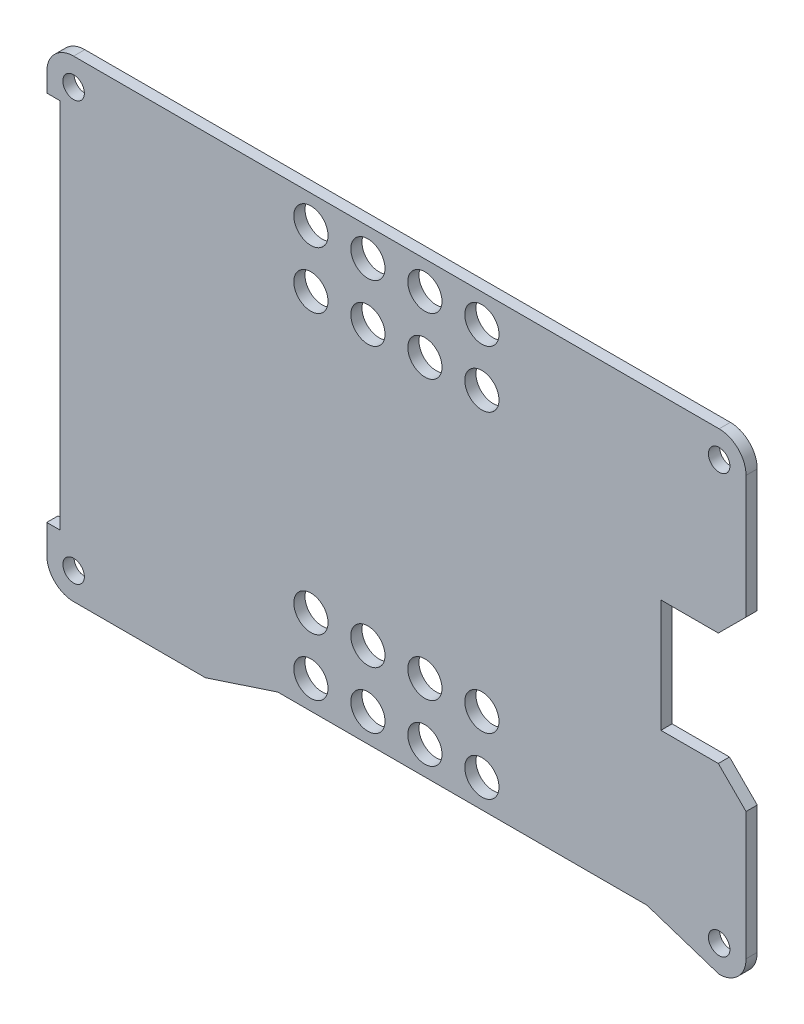
SolidWorks part; units mm, degrees
ref_plane "Front Plane" through (0, 0, 0) normal (0, 0, 1) x (1, 0, 0)
ref_plane "Top Plane" through (0, 0, 0) normal (0, 1, 0) x (1, 0, 0)
ref_plane "Right Plane" through (0, 0, 0) normal (1, 0, 0) x (0, 0, -1)
sketch "Sketch1" plane through (0, 0, 0) normal (0, 0, 1) x (1, 0, 0)
  line L0 (-301.9473, 111.7465) -> (-305.8779, 115.6771) construction
  line L1 (-305.8779, 115.6771) -> (-316.1078, 115.6771) construction
  line L2 (-316.1078, 115.6771) -> (-316.1078, 128.8851) construction
  line L3 (-316.1078, 128.8851) -> (-305.8779, 128.8851) construction
  line L4 (-305.8779, 128.8851) -> (-301.9473, 132.8157) construction
  line L5 (-301.9473, 132.8157) -> (-301.9473, 150.9704) construction
  line L6 (-305.7573, 154.7804) -> (-397.2471, 154.7804) construction
  line L7 (-401.0571, 150.9566) -> (-401.0571, 148.341) construction
  line L8 (-401.0571, 148.341) -> (-399.1521, 148.341) construction
  line L9 (-399.1521, 148.341) -> (-399.1521, 95.6449) construction
  line L10 (-399.1521, 95.6449) -> (-401.0571, 95.6449) construction
  line L11 (-401.0571, 95.6449) -> (-401.0571, 91.6593) construction
  line L12 (-397.2472, 87.8217) -> (-378.5565, 87.8217) construction
  line L13 (-378.5565, 87.8217) -> (-368.3165, 91.1883) construction
  line L14 (-368.3165, 91.1883) -> (-315.9973, 91.1883) construction
  line L15 (-315.9973, 91.1883) -> (-305.7573, 87.8217) construction
  line L16 (-301.9473, 91.6317) -> (-301.9473, 111.7465) construction
  line L17 (-301.9473, 111.7465) -> (-305.8779, 115.6771)
  line L18 (-305.8779, 115.6771) -> (-316.1078, 115.6771)
  line L19 (-316.1078, 115.6771) -> (-316.1078, 128.8851)
  line L20 (-316.1078, 128.8851) -> (-305.8779, 128.8851)
  line L21 (-305.8779, 128.8851) -> (-301.9473, 132.8157)
  line L22 (-301.9473, 132.8157) -> (-301.9473, 150.9704)
  line L23 (-305.7573, 154.7804) -> (-397.2471, 154.7804)
  line L24 (-401.0571, 150.9566) -> (-401.0571, 148.341)
  line L25 (-401.0571, 148.341) -> (-399.1521, 148.341)
  line L26 (-399.1521, 148.341) -> (-399.1521, 95.6449)
  line L27 (-399.1521, 95.6449) -> (-401.0571, 95.6449)
  line L28 (-401.0571, 95.6449) -> (-401.0571, 91.6593)
  line L29 (-397.2472, 87.8217) -> (-378.5565, 87.8217)
  line L30 (-378.5565, 87.8217) -> (-368.3165, 91.1883)
  line L31 (-368.3165, 91.1883) -> (-315.9973, 91.1883)
  line L32 (-315.9973, 91.1883) -> (-305.7573, 87.8217)
  line L33 (-301.9473, 91.6317) -> (-301.9473, 111.7465)
  circle A0 centre (-305.7573, 91.6317) radius 1.3559 construction
  circle A1 centre (-305.7573, 150.9704) radius 1.3559 construction
  circle A2 centre (-397.2471, 150.9704) radius 1.3559 construction
  circle A3 centre (-397.2472, 91.6317) radius 1.3559 construction
  circle A4 centre (-305.7573, 91.6317) radius 1.3559
  circle A5 centre (-305.7573, 150.9704) radius 1.3559
  circle A6 centre (-397.2471, 150.9704) radius 1.3559
  circle A7 centre (-397.2472, 91.6317) radius 1.3559
  arc A8 (-301.9473, 150.9704) -> (-305.7573, 154.7804) centre (-305.7573, 150.9704) ccw construction
  arc A9 (-397.2471, 154.7804) -> (-401.0571, 150.9566) centre (-397.2471, 150.9704) ccw construction
  arc A10 (-401.0571, 91.6593) -> (-397.2472, 87.8217) centre (-397.2472, 91.6317) ccw construction
  arc A11 (-305.7573, 87.8217) -> (-301.9473, 91.6317) centre (-305.7573, 91.6317) ccw construction
  arc A12 (-301.9473, 150.9704) -> (-305.7573, 154.7804) centre (-305.7573, 150.9704) ccw
  arc A13 (-397.2471, 154.7804) -> (-401.0571, 150.9566) centre (-397.2471, 150.9704) ccw
  arc A14 (-401.0571, 91.6593) -> (-397.2472, 87.8217) centre (-397.2472, 91.6317) ccw
  arc A15 (-305.7573, 87.8217) -> (-301.9473, 91.6317) centre (-305.7573, 91.6317) ccw
extrude "Boss-Extrude1" add sketch "Sketch1" along normal blind 1.5875
sketch "Sketch2" plane through (0, 0, 1.5875) normal (0, 0, 1) x (1, 0, 0)
  line L0 (-351.5022, 121.301) -> (-351.5022, 159.401) construction
  line L1 (-301.9473, 150.9704) -> (-301.9473, 91.6317) construction
  line L2 (-401.0571, 121.301) -> (-301.9473, 121.301) construction
  line L3 (-351.5022, 83.201) -> (-351.5022, 159.401) construction
  line L4 (-361.0272, 83.201) -> (-361.0272, 159.401)
  line L5 (-341.9772, 83.201) -> (-341.9772, 159.401)
  line L6 (-361.0272, 154.7804) -> (-341.9772, 154.7804)
  line L7 (-305.7573, 154.7804) -> (-397.2471, 154.7804) construction
  line L8 (-361.0272, 91.6317) -> (-341.9772, 91.6317)
  circle A0 centre (-351.5022, 159.401) radius 3.175
  arc A1 (-361.0272, 83.201) -> (-341.9772, 83.201) centre (-351.5022, 83.201) ccw
  arc A2 (-341.9772, 159.401) -> (-361.0272, 159.401) centre (-351.5022, 159.401) ccw
  circle A3 centre (-351.5022, 83.201) radius 3.175
  point P13 (-351.5022, 121.301)
  line M11 (-305.7573, 154.7804) -> (-397.2471, 154.7804)
  line M21 (-368.3165, 91.1883) -> (-315.9973, 91.1883)
  dimension "D1" = 6.35
  dimension "D2" = 38.1
  dimension "D3" = 19.05
extrude "Boss-Extrude2" [suppressed] add sketch "Sketch2" against normal blind 1.5875 contours L5 A2 L4 A0 M11 | L4 A1 L5 A3 M21
sketch "Sketch3" plane through (0, 0, 1.5875) normal (0, 0, 1) x (1, 0, 0)
  circle A0 centre (-397.2471, 150.9704) radius 1.524
  circle A1 centre (-305.7573, 150.9704) radius 1.524
  circle A2 centre (-305.7573, 91.6317) radius 1.524
  circle A3 centre (-397.2472, 91.6317) radius 1.524
  dimension "D1" = 3.048
extrude "Cut-Extrude1" cut sketch "Sketch3" against normal through all
sketch "Sketch4" plane through (0, 0, 1.5875) normal (0, 0, 1) x (1, 0, 0)
  line L0 (-301.9473, 133.571) -> (-305.8779, 129.6471)
  line L2 (-301.9473, 132.8157) -> (-301.9473, 150.9704) construction
  line L3 (-305.8779, 129.6471) -> (-314.0123, 129.6471)
  line L4 (-314.0123, 129.6471) -> (-314.0123, 113.6451)
  line L5 (-314.0123, 113.6451) -> (-305.8779, 113.6451)
  line L7 (-305.8779, 113.6451) -> (-301.9473, 109.7145)
  line L11 (-301.9473, 91.6317) -> (-301.9473, 111.7465) construction
  line L12 (-301.9473, 109.7145) -> (-301.9473, 133.571)
  dimension "D1" = 18.0828
  dimension "D2" = 16.002
  dimension "D3" = 8.1344
  dimension "D4" = 3.9306
  dimension "D5" = 23.8566
  dimension "D6" = 8.1344
  dimension "D7" = 5.5588
sketch "Sketch5" plane through (0, 0, 1.5875) normal (0, 0, 1) x (1, 0, 0)
  line L0 (-316.1078, 128.8851) -> (-305.8779, 128.8851) construction
  line L1 (-314.0123, 128.8851) -> (-316.1078, 128.8851)
  line L2 (-314.0123, 128.8851) -> (-314.0123, 115.6771)
  line L3 (-314.0123, 115.6771) -> (-316.1078, 115.6771)
  line L4 (-316.1078, 128.8851) -> (-316.1078, 115.6771)
  line L5 (-301.9473, 91.6317) -> (-301.9473, 111.7465) construction
  dimension "D1" = 12.065
extrude "Boss-Extrude3" add sketch "Sketch5" against normal up to vertex (1.5875 mm away) up to point (-316.1078, 128.8851, 0)
extrude "Cut-Extrude2" cut sketch "Sketch4" against normal through all
sketch "Sketch6" [suppressed] plane through (0, 0, 0) normal (0, 0, -1) x (-1, 0, 0)
  line L0 (351.5022, 154.7804) -> (351.5022, 91.1883) construction
  line L1 (368.3165, 91.1883) -> (315.9973, 91.1883) construction
  line L5 (305.7573, 154.7804) -> (397.2471, 154.7804) construction
  line L6 (379.7343, 158.5904) -> (379.7343, 154.7804)
  line L7 (379.7343, 154.7804) -> (386.7701, 154.7804)
  line L8 (386.7701, 154.7804) -> (386.7701, 158.5904)
  line L9 (347.9843, 87.3783) -> (347.9843, 91.1883)
  line L10 (347.9843, 91.1883) -> (355.0201, 91.1883)
  line L11 (355.0201, 91.1883) -> (355.0201, 87.3783)
  line L13 (316.2343, 154.7804) -> (316.2343, 158.5904)
  line L14 (323.2701, 154.7804) -> (316.2343, 154.7804)
  line L15 (323.2701, 158.5904) -> (323.2701, 154.7804)
  circle A0 centre (351.5022, 87.3783) radius 1.778
  circle A1 centre (351.5022, 87.3783) radius 3.5179
  circle A2 centre (383.2522, 158.5904) radius 3.5179
  circle A3 centre (383.2522, 158.5904) radius 1.778
  circle A4 centre (319.7522, 158.5904) radius 1.778
  circle A5 centre (319.7522, 158.5904) radius 3.5179
  dimension "D1" = 7.0358
  dimension "D2" = 7.0358
  dimension "D6" = 3.556
  dimension "D3" = 3.81
  dimension "D4" = 63.5
  dimension "D5" = 3.81
extrude "Boss-Extrude4" [suppressed] add sketch "Sketch6" against normal up to vertex
sketch "Sketch7" [suppressed] plane through (0, 0, 0) normal (0, 0, -1) x (-1, 0, 0)
  line L0 (397.2471, 154.7804) -> (397.2472, 87.8217) construction
  line L1 (308.0318, 158.801) -> (383.0318, 158.8011) construction
  line L2 (308.0318, 158.801) -> (308.0318, 83.801) construction
  line L3 (308.0318, 83.801) -> (383.0318, 83.801) construction
  line L4 (383.0318, 158.8011) -> (383.0318, 83.801) construction
  line L6 (397.2472, 121.301) -> (383.0318, 121.301) construction
  line L8 (304.4758, 158.801) -> (304.4758, 154.5584)
  line L9 (311.5878, 158.801) -> (311.5878, 154.7804)
  line L10 (305.7573, 154.7804) -> (397.2471, 154.7804) construction
  line L11 (379.4758, 158.8011) -> (379.4758, 154.7804)
  line L12 (386.5878, 158.8011) -> (386.5878, 154.7804)
  line L13 (386.5878, 154.7804) -> (379.4758, 154.7804)
  line L14 (379.4758, 83.801) -> (379.4758, 87.8217)
  line L15 (397.2472, 87.8217) -> (378.5565, 87.8217) construction
  line L16 (379.4758, 87.8217) -> (386.5878, 87.8217)
  line L17 (386.5878, 87.8217) -> (386.5878, 83.801)
  line L18 (304.4758, 83.801) -> (304.4758, 88.0437)
  line L19 (311.5878, 83.801) -> (311.5878, 89.7386)
  line L20 (315.9973, 91.1883) -> (305.7573, 87.8217) construction
  line L21 (301.9473, 133.571) -> (301.9473, 150.9704) construction
  circle A0 centre (308.0318, 158.801) radius 1.778
  circle A1 centre (383.0318, 158.8011) radius 1.778
  circle A2 centre (383.0318, 83.801) radius 1.778
  circle A3 centre (308.0318, 83.801) radius 1.778
  circle A4 centre (308.0318, 158.801) radius 3.556
  circle A5 centre (383.0318, 158.8011) radius 3.556
  circle A6 centre (308.0318, 83.801) radius 3.556
  circle A7 centre (383.0318, 83.801) radius 3.556
  arc A8 (305.7573, 154.7804) -> (301.9473, 150.9704) centre (305.7573, 150.9704) ccw construction
  arc A9 (301.9473, 91.6317) -> (305.7573, 87.8217) centre (305.7573, 91.6317) ccw construction
  arc M4 (301.9473, 91.6317) -> (305.7573, 87.8217) centre (305.7573, 91.6317) ccw
  line M5 (305.7573, 87.8217) -> (315.9973, 91.1883)
  line M8 (378.5565, 87.8217) -> (397.2472, 87.8217)
  line M16 (397.2471, 154.7804) -> (305.7573, 154.7804)
  arc M17 (305.7573, 154.7804) -> (301.9473, 150.9704) centre (305.7573, 150.9704) ccw
  dimension "D3" = 3.556
  dimension "D4" = 7.112
  dimension "D5" = 6.0845
  dimension "D1" = 75
  dimension "D2" = 75
extrude "Boss-Extrude5" [suppressed] add sketch "Sketch7" against normal blind 1.5875 contours A5 A1 | A5 L11 L12 M16 | A4 A0 | A4 L8 L9 M17 M16 | A6 L19 L18 M5 M4 | A6 A3 | A7 L17 L14 M8 | A7 A2
sketch "Sketch8" plane through (0, 0, 1.5875) normal (0, 0, 1) x (1, 0, 0)
  line L0 (-339.3864, 150.7799) -> (-363.618, 150.7799) construction
  line L1 (-351.5022, 150.7799) -> (-351.5022, 154.7804) construction
  line L2 (-305.7573, 154.7804) -> (-397.2471, 154.7804) construction
  line L3 (-363.618, 142.7027) -> (-339.3864, 142.7027) construction
  line L4 (-399.1521, 121.993) -> (-286.1871, 121.993) construction
  line L5 (-399.1521, 148.341) -> (-399.1521, 95.6449) construction
  line L7 (-368.3165, 91.1883) -> (-315.9973, 91.1883) construction
  line L8 (-363.618, 95.1888) -> (-339.3864, 95.1888) construction
  line L9 (-339.3864, 103.266) -> (-363.618, 103.266) construction
  circle A0 centre (-363.618, 150.7799) radius 2.4257
  circle A1 centre (-355.5408, 150.7799) radius 2.4257
  circle A2 centre (-347.4636, 150.7799) radius 2.4257
  circle A3 centre (-339.3864, 150.7799) radius 2.4257
  circle A4 centre (-339.3864, 142.7027) radius 2.4257
  circle A5 centre (-347.4636, 142.7027) radius 2.4257
  circle A6 centre (-355.5408, 142.7027) radius 2.4257
  circle A7 centre (-363.618, 142.7027) radius 2.4257
  circle A8 centre (-363.618, 95.1888) radius 2.4257
  circle A9 centre (-339.3864, 95.1888) radius 2.4257
  circle A10 centre (-347.4636, 95.1888) radius 2.4257
  circle A11 centre (-355.5408, 95.1888) radius 2.4257
  circle A12 centre (-363.618, 103.266) radius 2.4257
  circle A13 centre (-355.5408, 103.266) radius 2.4257
  circle A14 centre (-347.4636, 103.266) radius 2.4257
  circle A15 centre (-339.3864, 103.266) radius 2.4257
  dimension "D1" = 4.8514
  dimension "D2" = 3.2258
  dimension "D3" = 3.2258
  dimension "D4" = 3.2258
  dimension "D5" = 1.5748
  dimension "D6" = 3.2258
  dimension "D7" = 3.2258
  dimension "D8" = 1.5748
  dimension "D9" = 3.2258
extrude "Cut-Extrude3" cut sketch "Sketch8" against normal through all
